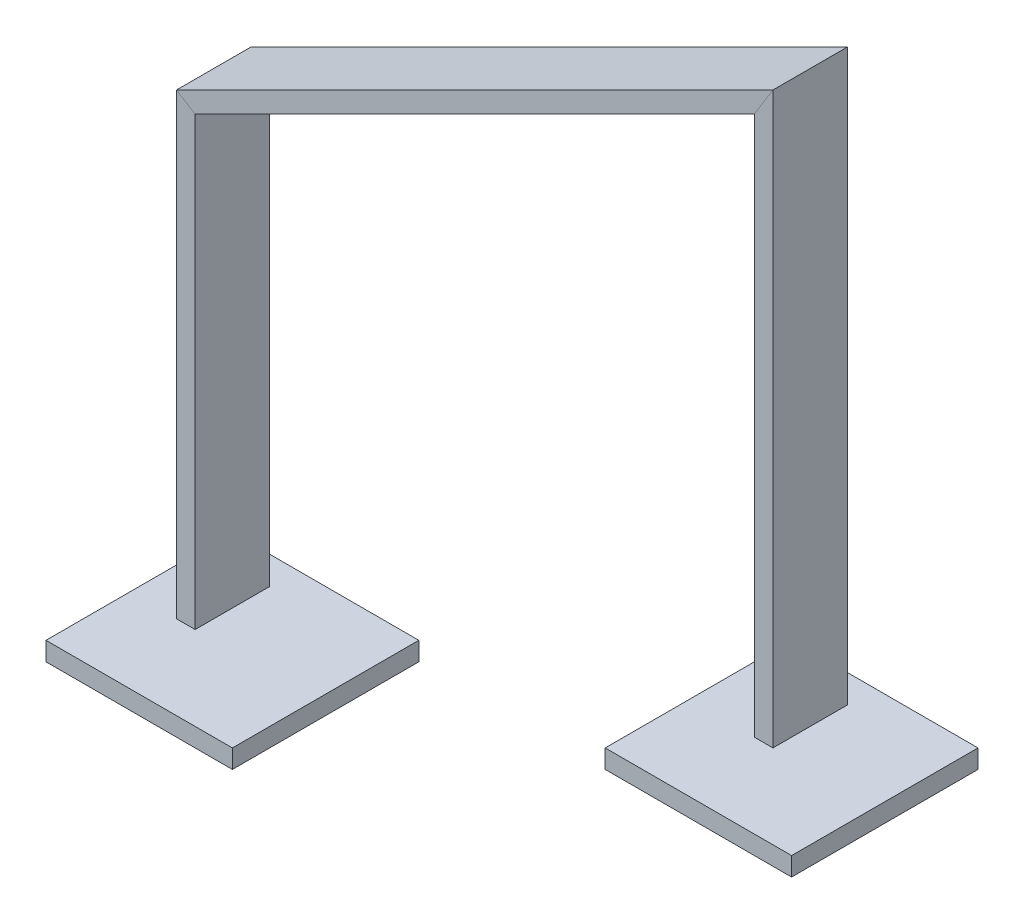
SolidWorks part; units mm, degrees
ref_plane "Front" through (0, 0, 0) normal (0, 0, 1) x (1, 0, 0)
ref_plane "Top" through (0, 0, 0) normal (0, 1, 0) x (1, 0, 0)
ref_plane "Right" through (0, 0, 0) normal (1, 0, 0) x (0, 0, -1)
sketch "Skizze1" plane through (0, 0, 0) normal (0, 1, 0) x (1, 0, 0)
  line L1 (0, -50) -> (100, -50)
  line L2 (0, -50) -> (0, 50)
  line L3 (0, 50) -> (100, 50)
  line L4 (100, -50) -> (100, 50)
  dimension "D1" = 100
  dimension "D2" = 50
  dimension "D3" = 0
extrude "Aufsatz-Linear austragen1" add sketch "Skizze1" along normal blind 10
sketch "Skizze2" plane through (0, 0, 0) normal (0, 0, 1) x (1, 0, 0)
  line L0 (0, 10) -> (100, 10) construction
  line L1 (300, 100) -> (400, 100)
  line L2 (300, 100) -> (300, 110)
  line L3 (300, 110) -> (400, 110)
  line L4 (400, 100) -> (400, 110)
  line L5 (100, 10) -> (100, 0) construction
  dimension "D1" = 10
  dimension "D2" = 100
  dimension "D3" = 100
  dimension "D4" = 300
extrude "Aufsatz-Linear austragen2" add sketch "Skizze2" along normal mid plane 100 separate body
sketch "Skizze3" plane through (0, 0, 0) normal (0, 0, 1) x (1, 0, 0)
  line L0 (50, 10) -> (50, 264.5085)
  line L1 (50, 264.5085) -> (350, 414.5085)
  line L2 (350, 414.5085) -> (350, 110)
  line L7 (100, 10) -> (300, 110) construction
  line L8 (0, 10) -> (100, 10) construction
  line L9 (400, 110) -> (300, 110) construction
  point P2 (0, 0)
  point P7 (0, 0)
  dimension "D5" = 250
sketch "Skizze4" plane through (0, 10, 0) normal (0, 1, 0) x (1, 0, 0)
  line L1 (50, -20) -> (40, -20)
  line L2 (50, -20) -> (50, 20)
  line L3 (50, 20) -> (40, 20)
  line L4 (40, -20) -> (40, 20)
  point P0 (50, 0)
  point P6 (50, 0)
  dimension "D1" = 40
  dimension "D2" = 10
sweep "Austragung1" add profiles "Skizze4" path "Skizze3"
other "Fläche verschieben1" face at (355, 110, 0) face at (45, 10, 0) parameters "D1"=15
